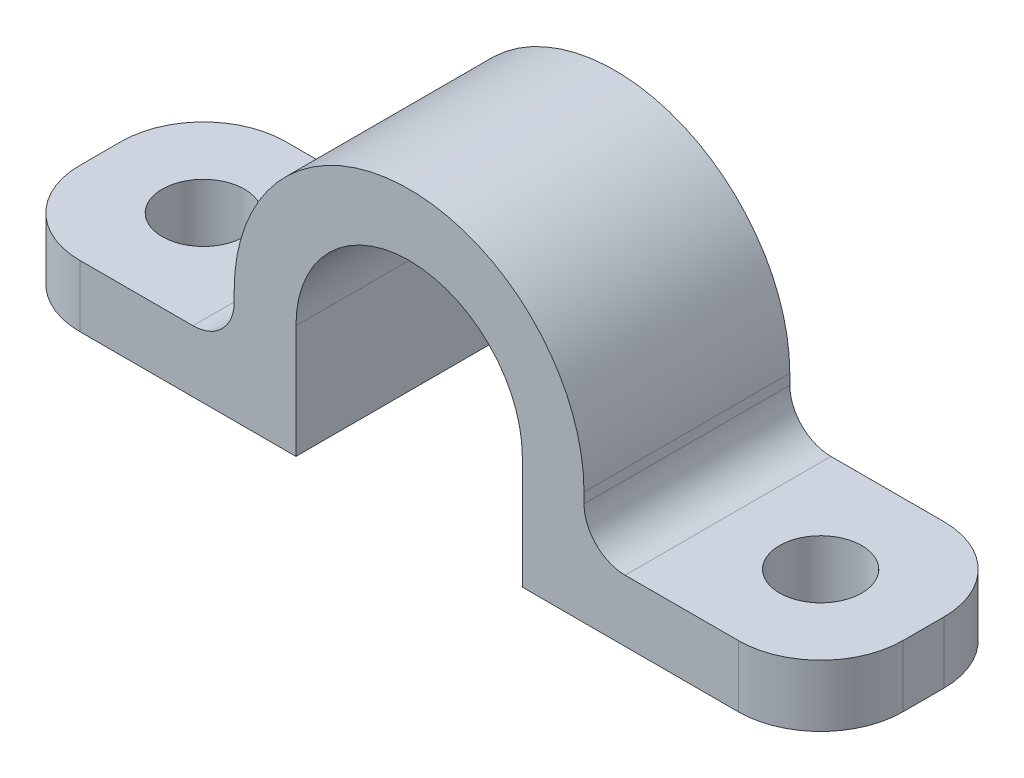
SolidWorks part; units mm, degrees
ref_plane "Front" through (0, 0, 0) normal (0, 0, 1) x (1, 0, 0)
ref_plane "Top" through (0, 0, 0) normal (0, 1, 0) x (1, 0, 0)
ref_plane "Right" through (0, 0, 0) normal (1, 0, 0) x (0, 0, -1)
sketch "Sketch1" plane through (0, 0, 0) normal (0, 0, 1) x (1, 0, 0)
  line L0 (-5.5, 0) -> (-5.5, -5.5)
  line L1 (-20, -2.5) -> (20, -2.5)
  line L2 (-20, -2.5) -> (-20, -5.5)
  line L3 (-20, -5.5) -> (20, -5.5)
  line L4 (20, -2.5) -> (20, -5.5)
  line L5 (5.5, 0) -> (5.5, -5.5)
  line L6 (-8.5, 0) -> (-8.5, -2.5)
  line L7 (8.5, 0) -> (8.5, -2.5)
  circle A0 centre (0, 0) radius 5.5
  circle A1 centre (0, 0) radius 8.5
  point P17 (0, -2.5)
  dimension "D2" = 11
  dimension "D1" = 3
  dimension "D3" = 20
  dimension "D4" = 3
extrude "Boss-Extrude1" add sketch "Sketch1" along normal mid plane 10 contours A1 L1 L0 A0 L5 | L1 A1 L3 L0 | A1 L1 L2 L3 | L3 A1 L1 L5 | A1 L3 L4 L1 | A1 L1 L7 | A1 L6 L1
sketch "Sketch2" plane through (0, -2.5, 0) normal (0, 1, 0) x (1, 0, 0)
  line L0 (0, 0) -> (0, 5) construction
  line L1 (8.5, 5) -> (-8.5, 5) construction
  circle A0 centre (-15, 0) radius 2
  circle A1 centre (15, 0) radius 2
  point P5 (0, 0)
  dimension "D1" = 4
  dimension "D2" = 15
extrude "Cut-Extrude1" cut sketch "Sketch2" against normal through all
fillet "Fillet1" radius 4 4 edges at (20, -4, -5) (20, -4, 5) (-20, -4, -5) (-20, -4, 5)
fillet "Fillet2" radius 2 2 edges at (8.5, -2.5, 0) (-8.5, -2.5, 0)
equation "\"D4@Sketch1\"=\"D1@Sketch1\""
